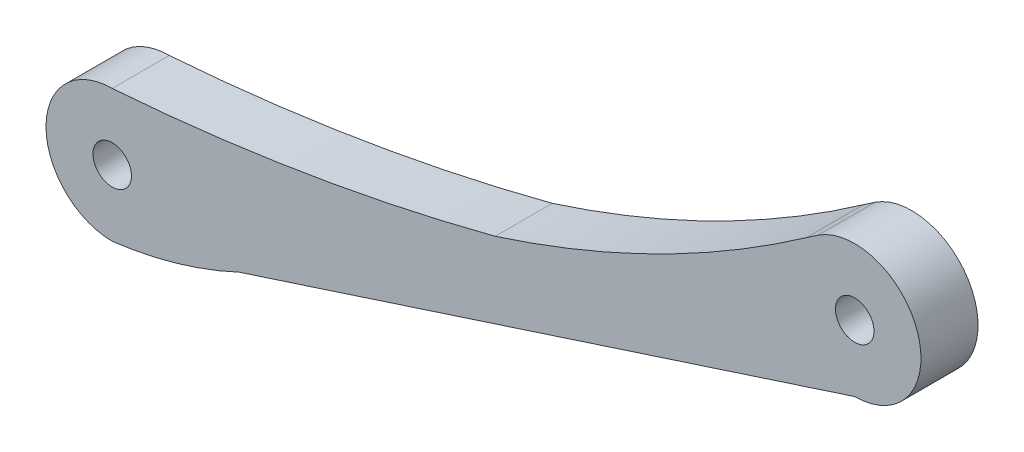
SolidWorks part; units mm, degrees
ref_plane "Front Plane" through (0, 0, 0) normal (0, 0, 1) x (1, 0, 0)
ref_plane "Top Plane" through (0, 0, 0) normal (0, 1, 0) x (1, 0, 0)
ref_plane "Right Plane" through (0, 0, 0) normal (1, 0, 0) x (0, 0, -1)
sketch "Sketch1" plane through (0, 0, 0) normal (0, 0, 1) x (1, 0, 0)
  line L1 (74.1564, 30.6771) -> (72.9384, 29.8474)
  line L2 (13.3235, -3.101) -> (78.02, 17.9272)
  arc A0 (78.02, 17.9272) -> (74.1564, 30.6771) centre (78.02, 24.8875) ccw
  circle A1 centre (0, 0) radius 2.023
  circle A2 centre (78.02, 24.8875) radius 2.024
  arc A3 (0, 6.9565) -> (0, -6.9565) centre (0, 0) ccw
  arc A6 (0, 6.9565) -> (40.2359, 13.6216) centre (-16.5, 231.3453) ccw
  arc A9 (0, -6.9565) -> (13.3235, -3.101) centre (-5.435, 36.7736) ccw
  arc A11 (40.2359, 13.6216) -> (72.9384, 29.8474) centre (3.5209, 128.6872) ccw
extrude "Boss-Extrude1" add sketch "Sketch1" along normal blind 6 contours A11 A6 A3 A9 L2 A0 L1 A2 A1
